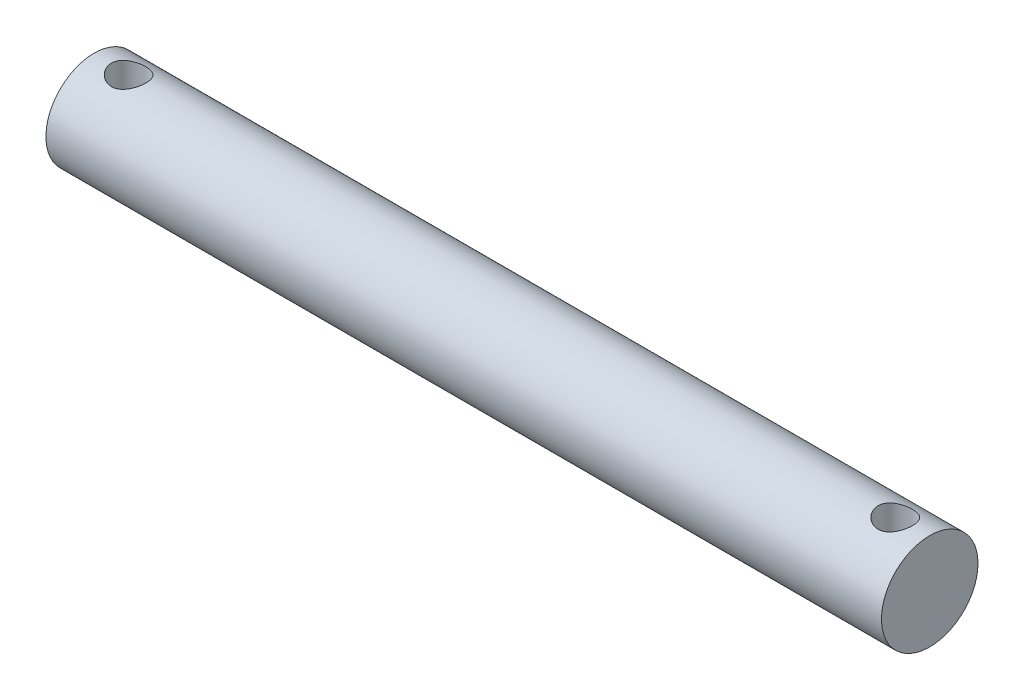
SolidWorks part; units mm, degrees
ref_plane "Front Plane" through (0, 0, 0) normal (0, 0, 1) x (1, 0, 0)
ref_plane "Top Plane" through (0, 0, 0) normal (0, 1, 0) x (1, 0, 0)
ref_plane "Right Plane" through (0, 0, 0) normal (1, 0, 0) x (0, 0, -1)
sketch "Sketch1" plane through (0, 0, 0) normal (1, 0, 0) x (0, 0, -1)
  circle A0 centre (0, 0) radius 4.445
  dimension "D1" = 8.89
extrude "Boss-Extrude1" add sketch "Sketch1" along normal mid plane 76.962
sketch "Sketch2" plane through (0, 0, 0) normal (0, 1, 0) x (1, 0, 0)
  line L0 (-38.481, 4.445) -> (-38.481, -4.445) construction
  line L1 (38.481, -4.445) -> (38.481, 4.445) construction
  circle A0 centre (-35.306, 0) radius 1.5875
  circle A1 centre (35.306, 0) radius 1.5875
  dimension "D3" = 3.175
  dimension "D1" = 3.175
  dimension "D2" = 3.175
extrude "Cut-Extrude1" cut sketch "Sketch2" against normal through all both and the other way through all
equation "\"D2@Sketch2\"=\"D1@Sketch2\""
